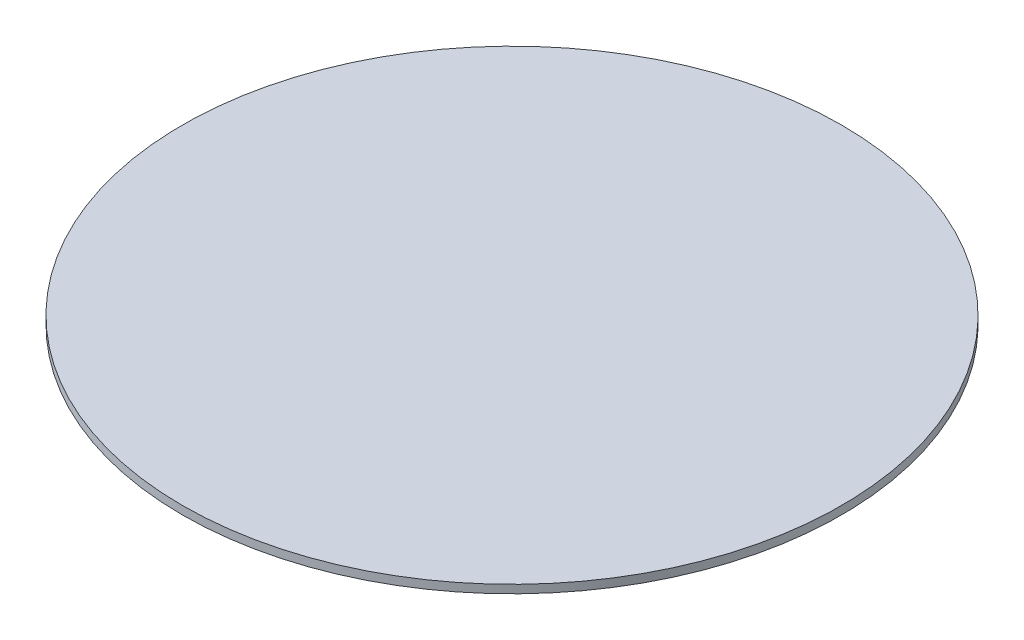
SolidWorks part; units mm, degrees
ref_plane "Front Plane" through (0, 0, 0) normal (0, 0, 1) x (1, 0, 0)
ref_plane "Top Plane" through (0, 0, 0) normal (0, 1, 0) x (1, 0, 0)
ref_plane "Right Plane" through (0, 0, 0) normal (1, 0, 0) x (0, 0, -1)
sketch "Sketch1" plane through (0, 0, 0) normal (0, 1, 0) x (1, 0, 0)
  line L0 (0, 0) -> (0, 107.95) construction
  circle A0 centre (0, 0) radius 127
  circle A1 centre (0, 0) radius 107.95 construction
  circle A2 centre (0, 107.95) radius 12.7 construction
  circle A3 centre (0, 107.95) radius 19.05 construction
  circle A4 centre (41.3107, 99.7328) radius 19.05 construction
  circle A5 centre (41.3107, 99.7328) radius 12.7 construction
  circle A6 centre (76.3322, 76.3322) radius 19.05 construction
  circle A7 centre (76.3322, 76.3322) radius 12.7 construction
  circle A8 centre (99.7328, 41.3107) radius 19.05 construction
  circle A9 centre (99.7328, 41.3107) radius 12.7 construction
  circle A10 centre (107.95, 0) radius 19.05 construction
  circle A11 centre (107.95, 0) radius 12.7 construction
  circle A12 centre (99.7328, -41.3107) radius 19.05 construction
  circle A13 centre (99.7328, -41.3107) radius 12.7 construction
  circle A14 centre (76.3322, -76.3322) radius 19.05 construction
  circle A15 centre (76.3322, -76.3322) radius 12.7 construction
  circle A16 centre (41.3107, -99.7328) radius 19.05 construction
  circle A17 centre (41.3107, -99.7328) radius 12.7 construction
  circle A18 centre (0, -107.95) radius 19.05 construction
  circle A19 centre (0, -107.95) radius 12.7 construction
  circle A20 centre (-41.3107, -99.7328) radius 19.05 construction
  circle A21 centre (-41.3107, -99.7328) radius 12.7 construction
  circle A22 centre (-76.3322, -76.3322) radius 19.05 construction
  circle A23 centre (-76.3322, -76.3322) radius 12.7 construction
  circle A24 centre (-99.7328, -41.3107) radius 19.05 construction
  circle A25 centre (-99.7328, -41.3107) radius 12.7 construction
  circle A26 centre (-107.95, 0) radius 19.05 construction
  circle A27 centre (-107.95, 0) radius 12.7 construction
  circle A28 centre (-99.7328, 41.3107) radius 19.05 construction
  circle A29 centre (-99.7328, 41.3107) radius 12.7 construction
  circle A30 centre (-76.3322, 76.3322) radius 19.05 construction
  circle A31 centre (-76.3322, 76.3322) radius 12.7 construction
  circle A32 centre (-41.3107, 99.7328) radius 19.05 construction
  circle A33 centre (-41.3107, 99.7328) radius 12.7 construction
  point P55 (0, 0)
  dimension "D1" = 254
  dimension "D2" = 25.4
  dimension "D3" = 38.1
  dimension "D4" = 19.05
  dimension "D6" = 41.3107
  dimension "D7" = 99.7328
  dimension "D5" = 16
extrude "Boss-Extrude1" add sketch "Sketch1" along normal blind 3.175
